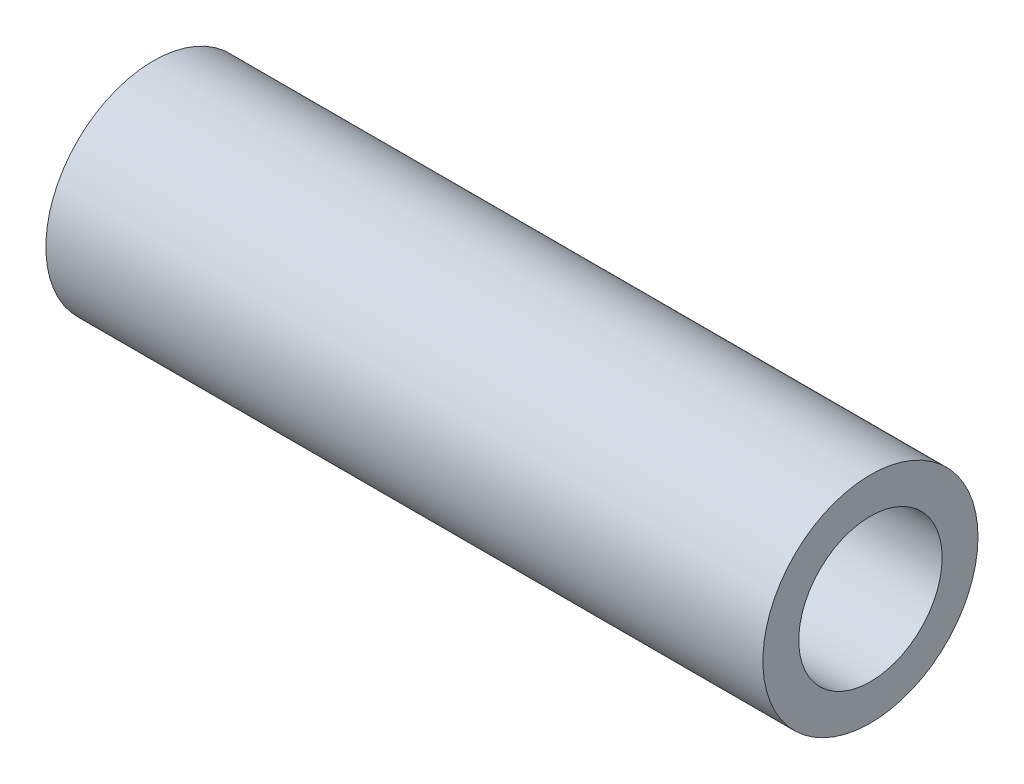
SolidWorks part; units mm, degrees
ref_plane "Front Plane" through (0, 0, 0) normal (0, 0, 1) x (1, 0, 0)
ref_plane "Top Plane" through (0, 0, 0) normal (0, 1, 0) x (1, 0, 0)
ref_plane "Right Plane" through (0, 0, 0) normal (1, 0, 0) x (0, 0, -1)
sketch "Sketch1" plane through (0, 0, 0) normal (1, 0, 0) x (0, 0, -1)
  circle A0 centre (0, 0) radius 1.5
  circle A1 centre (0, 0) radius 1
  dimension "D1" = 3
  dimension "D2" = 2
extrude "9811T16" add sketch "Sketch1" along normal blind 10
sketch "Sketch2" plane through (0, 0, 0) normal (0, 1, 0) x (1, 0, 0)
  line L0 (0, 1.5) -> (0, -1.5) construction
  line L1 (0, 1.5) -> (0, -1.5) construction
  line L2 (0, 0) -> (7.3094, 0) construction
  circle A0 centre (7.3094, 0) radius 0.889
  dimension "D1" = 1.778
